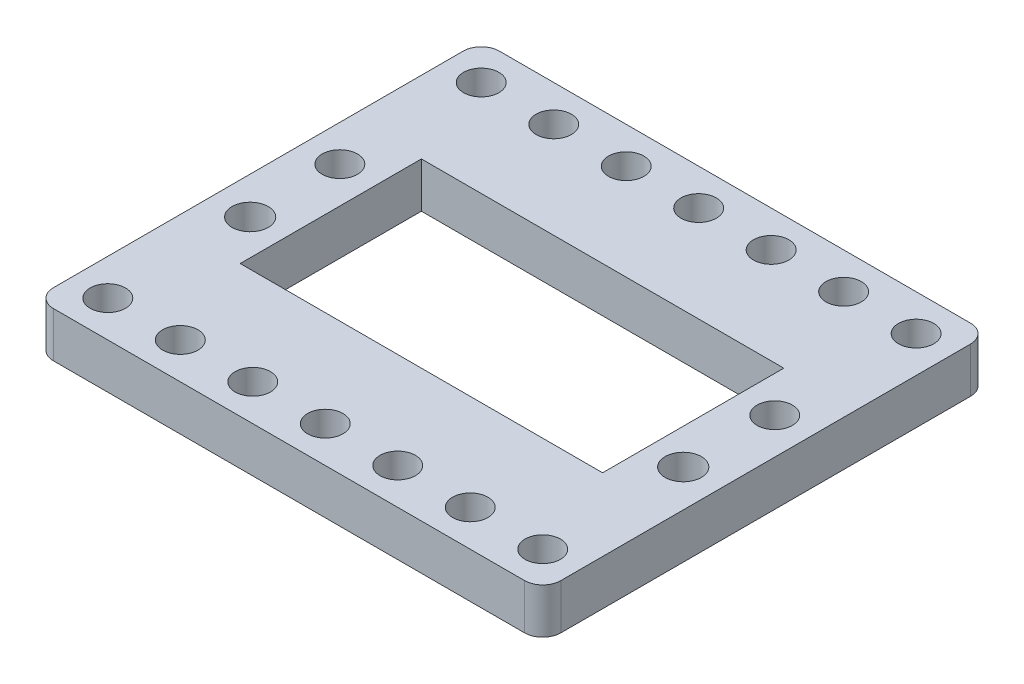
SolidWorks part; units mm, degrees
ref_plane "Front Plane" through (0, 0, 0) normal (0, 0, 1) x (1, 0, 0)
ref_plane "Top Plane" through (0, 0, 0) normal (0, 1, 0) x (1, 0, 0)
ref_plane "Right Plane" through (0, 0, 0) normal (1, 0, 0) x (0, 0, -1)
sketch "Sketch1" plane through (0, 0, 0) normal (0, 1, 0) x (1, 0, 0)
  line L1 (2, 0) -> (98, 0)
  line L2 (0, -2) -> (0, -47.22)
  line L3 (2, -49.22) -> (98, -49.22)
  line L4 (100, -2) -> (100, -47.22)
  arc A0 (98, -49.22) -> (100, -47.22) centre (98, -47.22) ccw
  arc A1 (0, -47.22) -> (2, -49.22) centre (2, -47.22) ccw
  arc A2 (2, 0) -> (0, -2) centre (2, -2) ccw
  arc A3 (98, 0) -> (100, -2) centre (98, -2) cw
  point P7 (100, -49.22)
  point P12 (0, 0)
  point P15 (100, 0)
  dimension "D3" = 2
  dimension "D1" = 100
  dimension "D2" = 49.22
extrude "Boss-Extrude1" add sketch "Sketch1" along normal blind 5
sketch "Sketch2" plane through (0, 5, 0) normal (0, 1, 0) x (1, 0, 0)
  line L1 (100, -47.22) -> (100, -2) construction
  line L2 (90, -4.0048) -> (0, -4.0048) construction
  line L3 (0, -2) -> (0, -47.22) construction
  line L4 (90, -45.22) -> (0, -45.22) construction
  line L6 (30, -24.61) -> (70, -24.61) construction
  line L7 (30, -14.61) -> (70, -14.61)
  line L8 (30, -14.61) -> (30, -34.61)
  line L9 (30, -34.61) -> (70, -34.61)
  line L10 (70, -14.61) -> (70, -34.61)
  line L11 (98, 0) -> (2, 0) construction
  line L12 (2, -49.22) -> (98, -49.22) construction
  line L13 (50, -14.61) -> (50, -34.61) construction
  circle A0 centre (90, -4.0048) radius 1.95
  circle A1 centre (82, -4.0048) radius 1.95
  circle A2 centre (18, -4.0048) radius 1.95
  circle A3 centre (26, -4.0048) radius 1.95
  circle A4 centre (34, -4.0048) radius 1.95
  circle A5 centre (42, -4.0048) radius 1.95
  circle A6 centre (50, -4.0048) radius 1.95
  circle A7 centre (58, -4.0048) radius 1.95
  circle A8 centre (66, -4.0048) radius 1.95
  circle A9 centre (74, -4.0048) radius 1.95
  circle A10 centre (90, -45.22) radius 1.95
  circle A11 centre (82, -45.22) radius 1.95
  circle A12 centre (18, -45.22) radius 1.95
  circle A13 centre (26, -45.22) radius 1.95
  circle A14 centre (34, -45.22) radius 1.95
  circle A15 centre (42, -45.22) radius 1.95
  circle A16 centre (50, -45.22) radius 1.95
  circle A17 centre (58, -45.22) radius 1.95
  circle A18 centre (66, -45.22) radius 1.95
  circle A19 centre (74, -45.22) radius 1.95
  dimension "D1" = 3.9
  dimension "D4" = 3.9
  dimension "D7" = 3.9
  dimension "D8" = 3.9
  dimension "D9" = 3.9
  dimension "D10" = 3.9
  dimension "D11" = 3.9
  dimension "D12" = 3.9
  dimension "D13" = 3.9
  dimension "D14" = 3.9
  dimension "D22" = 3.9
  dimension "D23" = 3.9
  dimension "D25" = 3.9
  dimension "D26" = 3.9
  dimension "D27" = 3.9
  dimension "D28" = 3.9
  dimension "D29" = 3.9
  dimension "D30" = 3.9
  dimension "D31" = 3.9
  dimension "D32" = 3.9
  dimension "D5" = 8
  dimension "D6" = 18
  dimension "D15" = 8
  dimension "D16" = 8
  dimension "D17" = 8
  dimension "D18" = 8
  dimension "D19" = 8
  dimension "D20" = 8
  dimension "D21" = 8
  dimension "D24" = 8
  dimension "D33" = 8
  dimension "D34" = 8
  dimension "D35" = 8
  dimension "D36" = 8
  dimension "D37" = 8
  dimension "D38" = 8
  dimension "D39" = 8
  dimension "D40" = 4.0048
  dimension "D41" = 10
  dimension "D42" = 18
  dimension "D43" = 40
  dimension "D44" = 20
  dimension "D46" = 4
  dimension "D47" = 10
extrude "Cut-Extrude1" cut sketch "Sketch2" against normal through all
sketch "Sketch4" plane through (0, 5, 0) normal (0, 1, 0) x (1, 0, 0)
  line L0 (98, 0) -> (2, 0) construction
  line L1 (78, 0) -> (100, 0)
  line L2 (78, 0) -> (78, -49.22)
  line L3 (78, -49.22) -> (100, -49.22)
  line L4 (100, 0) -> (100, -49.22)
  line L5 (2, -49.22) -> (98, -49.22) construction
  line L6 (100, -47.22) -> (100, -2) construction
  line L8 (0, 0) -> (22, 0)
  line L9 (0, 0) -> (0, -49.22)
  line L10 (0, -49.22) -> (22, -49.22)
  line L11 (22, 0) -> (22, -49.22)
  dimension "D1" = 22
  dimension "D2" = 22
extrude "Cut-Extrude2" cut sketch "Sketch4" against normal blind 10
fillet "Fillet1" radius 2 1 edges at (22, 2.5, 0)
fillet "Fillet2" radius 2 1 edges at (22, 2.5, 49.22)
fillet "Fillet3" radius 2 1 edges at (78, 2.5, 49.22)
fillet "Fillet4" radius 2 1 edges at (78, 2.5, 0)
sketch "Sketch5" plane through (0, 5, 0) normal (0, 1, 0) x (1, 0, 0)
  line L0 (22, -24.61) -> (78, -24.61) construction
  line L1 (78, -2) -> (78, -47.22) construction
  line L3 (70, -14.61) -> (30, -14.61) construction
  line L4 (22, -47.22) -> (22, -2) construction
  line L5 (74, -19.6103) -> (73.9, -29.6097) construction
  line L6 (26, -19.6103) -> (26.1, -29.6097) construction
  line L7 (30, -14.61) -> (30, -34.61) construction
  line L8 (70, -34.61) -> (70, -14.61) construction
  line L9 (30, -34.61) -> (70, -34.61) construction
  circle A0 centre (74, -19.6103) radius 1.95
  circle A1 centre (73.9, -29.6097) radius 2
  circle A2 centre (26, -19.6103) radius 1.95
  circle A3 centre (26.1, -29.6097) radius 2
  point P17 (73.95, -24.61)
  point P18 (26.05, -24.61)
  dimension "D1" = 3.9
  dimension "D4" = 4
  dimension "D7" = 3.9
  dimension "D8" = 4
  dimension "D2" = 4
  dimension "D3" = 3.9
  dimension "D5" = 10
  dimension "D6" = 4
  dimension "D9" = 10
  dimension "D10" = 3.9
extrude "Cut-Extrude3" cut sketch "Sketch5" against normal through all
